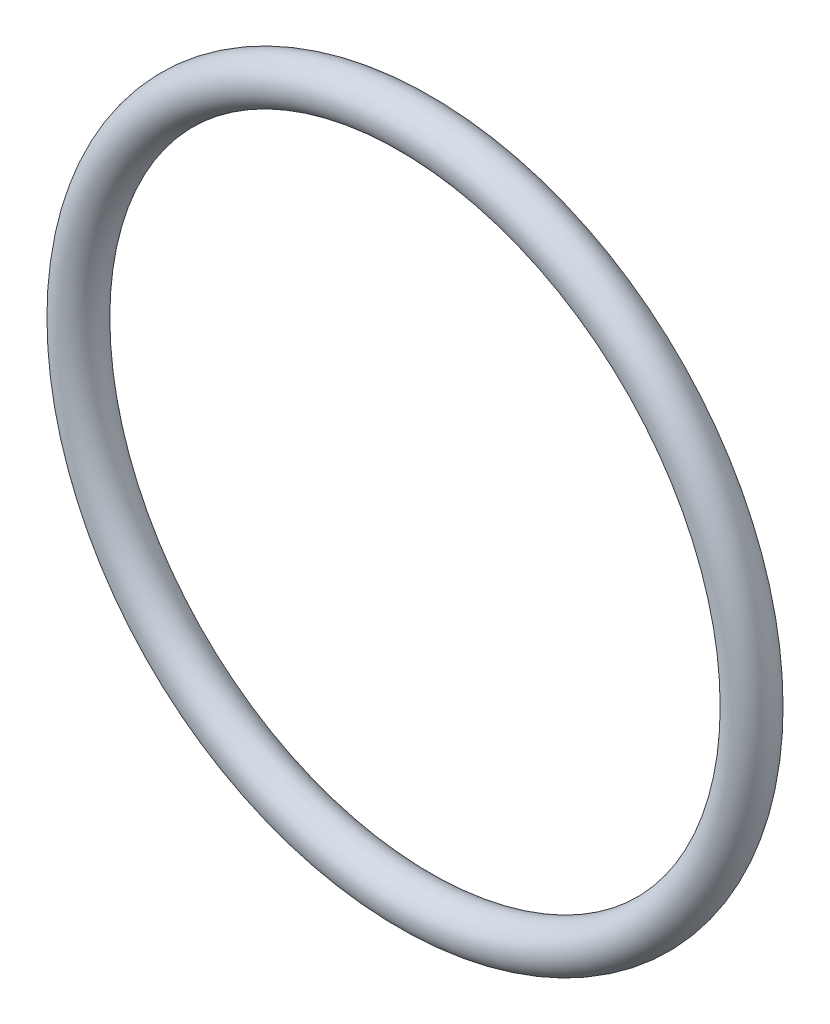
SolidWorks part; units mm, degrees
ref_plane "Front" through (0, 0, 0) normal (0, 0, 1) x (1, 0, 0)
ref_plane "Top" through (0, 0, 0) normal (0, 1, 0) x (1, 0, 0)
ref_plane "Right" through (0, 0, 0) normal (1, 0, 0) x (0, 0, -1)
sketch "Sketch1" plane through (0, 0, 0) normal (1, 0, 0) x (0, -1, 0)
  line L0 (0, -0.889) -> (0, 0.889) construction
  line L2 (-15.7721, 0) -> (15.7721, 0) construction
  line L3 (-12.5603, 0) -> (12.5603, 0) construction
  circle A0 centre (13.4493, 0) radius 0.889
  point P9 (12.5603, 0)
  point P10 (14.3383, 0)
  point P13 (13.4493, 0.889)
  point P14 (13.4493, -0.889)
  dimension "Width" = 1.778
  dimension "ID" = 25.1206
revolve "Revolve1" add sketch "Sketch1" angle 360 about L0
